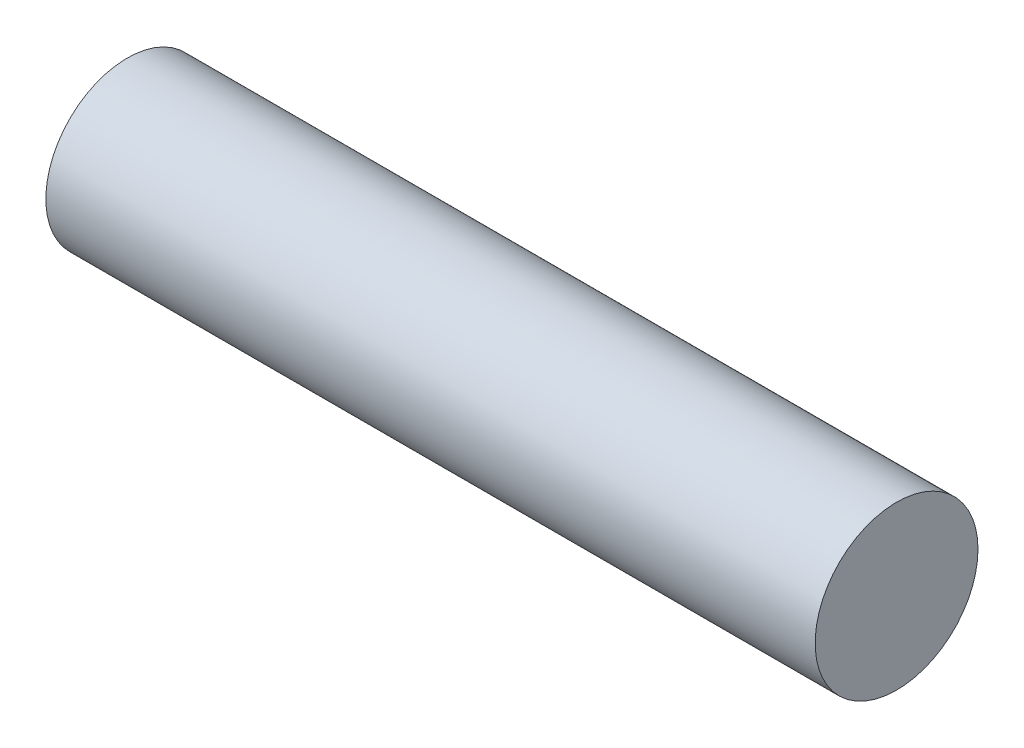
SolidWorks part; units mm, degrees
ref_plane "Plan de face" through (0, 0, 0) normal (0, 0, 1) x (1, 0, 0)
ref_plane "Plan de dessus" through (0, 0, 0) normal (0, 1, 0) x (1, 0, 0)
ref_plane "Plan de droite" through (0, 0, 0) normal (1, 0, 0) x (0, 0, -1)
sketch "Esquisse1" plane through (0, 0, 0) normal (0, 0, 1) x (1, 0, 0)
  line L0 (-30.902, 0) -> (-0.902, 0)
sweep "Balayage1" add path "Esquisse1" circular profile diameter 6.35 parameters "D3"=6.35
